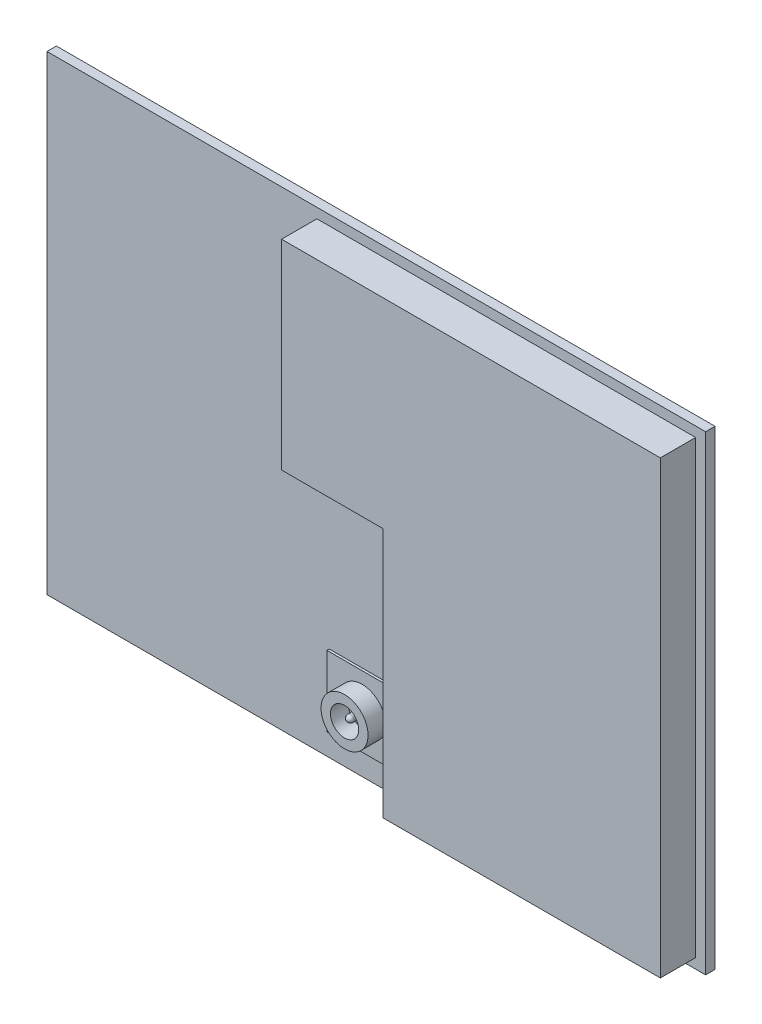
SolidWorks part; units mm, degrees
ref_plane "Front Plane" through (0, 0, 0) normal (0, 0, 1) x (1, 0, 0)
ref_plane "Top Plane" through (0, 0, 0) normal (0, 1, 0) x (1, 0, 0)
ref_plane "Right Plane" through (0, 0, 0) normal (1, 0, 0) x (0, 0, -1)
sketch "Sketch1" plane through (0, 0, 0) normal (0, 0, 1) x (1, 0, 0)
  line L1 (0, 0) -> (28, 0)
  line L2 (0, 0) -> (0, 20)
  line L3 (0, 20) -> (28, 20)
  line L4 (28, 0) -> (28, 20)
  dimension "D1" = 28
  dimension "D2" = 20
extrude "Boss-Extrude1" add sketch "Sketch1" along normal blind 0.4
sketch "Sketch2" plane through (0, 0, 0.4) normal (0, 0, 1) x (1, 0, 0)
  line L0 (11.475, 11.075) -> (15.775, 11.075)
  line L1 (27.575, 19.575) -> (11.475, 19.575)
  line L2 (27.575, 19.575) -> (27.575, 0.425)
  line L3 (27.575, 0.425) -> (15.775, 0.425)
  line L4 (11.475, 19.575) -> (11.475, 11.075)
  line L5 (15.775, 11.075) -> (15.775, 0.425)
  line L6 (0, 10) -> (28, 10) construction
  line L7 (0, 20) -> (0, 0) construction
  line L8 (28, 0) -> (28, 20) construction
  point P12 (27.575, 10)
  dimension "D1" = 19.15
  dimension "D2" = 11.8
  dimension "D3" = 0.425
  dimension "D4" = 16.1
  dimension "D5" = 8.5
extrude "Boss-Extrude2" add sketch "Sketch2" along normal blind 1.5
sketch "Sketch3" plane through (0, 0, 0.4) normal (0, 0, 1) x (1, 0, 0)
  line L0 (0, 0) -> (28, 0) construction
  line L1 (12, 4) -> (15, 4)
  line L2 (12, 4) -> (12, 1)
  line L3 (12, 1) -> (15, 1)
  line L4 (15, 4) -> (15, 1)
  line L5 (0, 20) -> (0, 0) construction
  dimension "D1" = 3
  dimension "D2" = 3
  dimension "D3" = 1
  dimension "D4" = 12
extrude "Boss-Extrude3" add sketch "Sketch3" along normal blind 0.1
sketch "Sketch4" plane through (0, 0, 0.5) normal (0, 0, 1) x (1, 0, 0)
  line L0 (13.5, 4) -> (13.5, 1) construction
  line L1 (15, 4) -> (12, 4) construction
  line L2 (12, 1) -> (15, 1) construction
  circle A0 centre (13.5, 2.5) radius 1
  circle A1 centre (13.5, 2.5) radius 0.6
  dimension "D1" = 2
  dimension "D2" = 1.2
extrude "Boss-Extrude4" add sketch "Sketch4" along normal blind 0.75
sketch "Sketch5" plane through (0, 0, 0.5) normal (0, 0, 1) x (1, 0, 0)
  circle A0 centre (13.5, 2.5) radius 0.15
  dimension "D1" = 0.3
extrude "Boss-Extrude5" add sketch "Sketch5" along normal blind 0.65
fillet "Fillet1" radius 0.15 1 edges at (13.65, 2.5, 1.15)
sketch "Sketch6" plane through (0, 0, 0) normal (0, 0, -1) x (-1, 0, 0)
  line L0 (0, 0) -> (-28, 0) construction
  line L1 (-12.8, 0.3) -> (-12.2, 0.3)
  line L2 (-12.8, 0.3) -> (-12.8, 1.1)
  line L3 (-12.8, 1.1) -> (-12.2, 1.1)
  line L4 (-12.2, 0.3) -> (-12.2, 1.1)
  line L5 (-28, 0) -> (-28, 20) construction
  line L6 (0, 20) -> (0, 0) construction
  line L7 (-13.8, 0.3) -> (-13.2, 0.3)
  line L8 (-13.8, 0.3) -> (-13.8, 1.1)
  line L9 (-13.8, 1.1) -> (-13.2, 1.1)
  line L10 (-13.2, 0.3) -> (-13.2, 1.1)
  line L11 (-14.8, 0.3) -> (-14.2, 0.3)
  line L12 (-14.8, 0.3) -> (-14.8, 1.1)
  line L13 (-14.8, 1.1) -> (-14.2, 1.1)
  line L14 (-14.2, 0.3) -> (-14.2, 1.1)
  line L15 (-15.8, 0.3) -> (-15.2, 0.3)
  line L16 (-15.8, 0.3) -> (-15.8, 1.1)
  line L17 (-15.8, 1.1) -> (-15.2, 1.1)
  line L18 (-15.2, 0.3) -> (-15.2, 1.1)
  line L19 (-16.8, 0.3) -> (-16.2, 0.3)
  line L20 (-16.8, 0.3) -> (-16.8, 1.1)
  line L21 (-16.8, 1.1) -> (-16.2, 1.1)
  line L22 (-16.2, 0.3) -> (-16.2, 1.1)
  line L23 (-17.8, 0.3) -> (-17.2, 0.3)
  line L24 (-17.8, 0.3) -> (-17.8, 1.1)
  line L25 (-17.8, 1.1) -> (-17.2, 1.1)
  line L26 (-17.2, 0.3) -> (-17.2, 1.1)
  line L27 (-18.8, 0.3) -> (-18.2, 0.3)
  line L28 (-18.8, 0.3) -> (-18.8, 1.1)
  line L29 (-18.8, 1.1) -> (-18.2, 1.1)
  line L30 (-18.2, 0.3) -> (-18.2, 1.1)
  line L31 (-19.8, 0.3) -> (-19.2, 0.3)
  line L32 (-19.8, 0.3) -> (-19.8, 1.1)
  line L33 (-19.8, 1.1) -> (-19.2, 1.1)
  line L34 (-19.2, 0.3) -> (-19.2, 1.1)
  line L35 (-20.8, 0.3) -> (-20.2, 0.3)
  line L36 (-20.8, 0.3) -> (-20.8, 1.1)
  line L37 (-20.8, 1.1) -> (-20.2, 1.1)
  line L38 (-20.2, 0.3) -> (-20.2, 1.1)
  line L39 (-21.8, 0.3) -> (-21.2, 0.3)
  line L40 (-21.8, 0.3) -> (-21.8, 1.1)
  line L41 (-21.8, 1.1) -> (-21.2, 1.1)
  line L42 (-21.2, 0.3) -> (-21.2, 1.1)
  line L43 (-22.8, 0.3) -> (-22.2, 0.3)
  line L44 (-22.8, 0.3) -> (-22.8, 1.1)
  line L45 (-22.8, 1.1) -> (-22.2, 1.1)
  line L46 (-22.2, 0.3) -> (-22.2, 1.1)
  line L47 (-23.8, 0.3) -> (-23.2, 0.3)
  line L48 (-23.8, 0.3) -> (-23.8, 1.1)
  line L49 (-23.8, 1.1) -> (-23.2, 1.1)
  line L50 (-23.2, 0.3) -> (-23.2, 1.1)
  line L51 (-24.8, 0.3) -> (-24.2, 0.3)
  line L52 (-24.8, 0.3) -> (-24.8, 1.1)
  line L53 (-24.8, 1.1) -> (-24.2, 1.1)
  line L54 (-24.2, 0.3) -> (-24.2, 1.1)
  line L55 (-25.8, 0.3) -> (-25.2, 0.3)
  line L56 (-25.8, 0.3) -> (-25.8, 1.1)
  line L57 (-25.8, 1.1) -> (-25.2, 1.1)
  line L58 (-25.2, 0.3) -> (-25.2, 1.1)
  line L59 (-26.8, 0.3) -> (-26.2, 0.3)
  line L60 (-26.8, 0.3) -> (-26.8, 1.1)
  line L61 (-26.8, 1.1) -> (-26.2, 1.1)
  line L62 (-26.2, 0.3) -> (-26.2, 1.1)
  line L63 (-13.8, 18.9) -> (-13.2, 18.9)
  line L64 (-13.8, 18.9) -> (-13.8, 19.7)
  line L65 (-13.8, 19.7) -> (-13.2, 19.7)
  line L66 (-13.2, 18.9) -> (-13.2, 19.7)
  line L67 (-14.8, 18.9) -> (-14.2, 18.9)
  line L68 (-14.8, 18.9) -> (-14.8, 19.7)
  line L69 (-14.8, 19.7) -> (-14.2, 19.7)
  line L70 (-14.2, 18.9) -> (-14.2, 19.7)
  line L71 (-15.8, 18.9) -> (-15.2, 18.9)
  line L72 (-15.8, 18.9) -> (-15.8, 19.7)
  line L73 (-15.8, 19.7) -> (-15.2, 19.7)
  line L74 (-15.2, 18.9) -> (-15.2, 19.7)
  line L75 (-16.8, 18.9) -> (-16.2, 18.9)
  line L76 (-16.8, 18.9) -> (-16.8, 19.7)
  line L77 (-16.8, 19.7) -> (-16.2, 19.7)
  line L78 (-16.2, 18.9) -> (-16.2, 19.7)
  line L79 (-17.8, 18.9) -> (-17.2, 18.9)
  line L80 (-17.8, 18.9) -> (-17.8, 19.7)
  line L81 (-17.8, 19.7) -> (-17.2, 19.7)
  line L82 (-17.2, 18.9) -> (-17.2, 19.7)
  line L83 (-18.8, 18.9) -> (-18.2, 18.9)
  line L84 (-18.8, 18.9) -> (-18.8, 19.7)
  line L85 (-18.8, 19.7) -> (-18.2, 19.7)
  line L86 (-18.2, 18.9) -> (-18.2, 19.7)
  line L87 (-19.8, 18.9) -> (-19.2, 18.9)
  line L88 (-19.8, 18.9) -> (-19.8, 19.7)
  line L89 (-19.8, 19.7) -> (-19.2, 19.7)
  line L90 (-19.2, 18.9) -> (-19.2, 19.7)
  line L91 (-20.8, 18.9) -> (-20.2, 18.9)
  line L92 (-20.8, 18.9) -> (-20.8, 19.7)
  line L93 (-20.8, 19.7) -> (-20.2, 19.7)
  line L94 (-20.2, 18.9) -> (-20.2, 19.7)
  line L95 (-21.8, 18.9) -> (-21.2, 18.9)
  line L96 (-21.8, 18.9) -> (-21.8, 19.7)
  line L97 (-21.8, 19.7) -> (-21.2, 19.7)
  line L98 (-21.2, 18.9) -> (-21.2, 19.7)
  line L99 (-22.8, 18.9) -> (-22.2, 18.9)
  line L100 (-22.8, 18.9) -> (-22.8, 19.7)
  line L101 (-22.8, 19.7) -> (-22.2, 19.7)
  line L102 (-22.2, 18.9) -> (-22.2, 19.7)
  line L103 (-23.8, 18.9) -> (-23.2, 18.9)
  line L104 (-23.8, 18.9) -> (-23.8, 19.7)
  line L105 (-23.8, 19.7) -> (-23.2, 19.7)
  line L106 (-23.2, 18.9) -> (-23.2, 19.7)
  line L107 (-24.8, 18.9) -> (-24.2, 18.9)
  line L108 (-24.8, 18.9) -> (-24.8, 19.7)
  line L109 (-24.8, 19.7) -> (-24.2, 19.7)
  line L110 (-24.2, 18.9) -> (-24.2, 19.7)
  line L111 (-25.8, 18.9) -> (-25.2, 18.9)
  line L112 (-25.8, 18.9) -> (-25.8, 19.7)
  line L113 (-25.8, 19.7) -> (-25.2, 19.7)
  line L114 (-25.2, 18.9) -> (-25.2, 19.7)
  line L115 (-26.8, 18.9) -> (-26.2, 18.9)
  line L116 (-26.8, 18.9) -> (-26.8, 19.7)
  line L117 (-26.8, 19.7) -> (-26.2, 19.7)
  line L118 (-26.2, 18.9) -> (-26.2, 19.7)
  line L119 (-12.8, 18.9) -> (-12.2, 18.9)
  line L120 (-12.8, 18.9) -> (-12.8, 19.7)
  line L121 (-12.8, 19.7) -> (-12.2, 19.7)
  line L122 (-12.2, 18.9) -> (-12.2, 19.7)
  line L123 (-27.7, 2.3) -> (-26.9, 2.3)
  line L124 (-27.7, 2.3) -> (-27.7, 1.7)
  line L125 (-27.7, 1.7) -> (-26.9, 1.7)
  line L126 (-26.9, 2.3) -> (-26.9, 1.7)
  line L127 (-12.2, 2.3) -> (-11.4, 2.3)
  line L128 (-12.2, 2.3) -> (-12.2, 1.7)
  line L129 (-12.2, 1.7) -> (-11.4, 1.7)
  line L130 (-11.4, 2.3) -> (-11.4, 1.7)
  line L131 (-12.2, 3.3) -> (-11.4, 3.3)
  line L132 (-12.2, 3.3) -> (-12.2, 2.7)
  line L133 (-12.2, 2.7) -> (-11.4, 2.7)
  line L134 (-11.4, 3.3) -> (-11.4, 2.7)
  line L135 (-12.2, 4.3) -> (-11.4, 4.3)
  line L136 (-12.2, 4.3) -> (-12.2, 3.7)
  line L137 (-12.2, 3.7) -> (-11.4, 3.7)
  line L138 (-11.4, 4.3) -> (-11.4, 3.7)
  line L139 (-12.2, 5.3) -> (-11.4, 5.3)
  line L140 (-12.2, 5.3) -> (-12.2, 4.7)
  line L141 (-12.2, 4.7) -> (-11.4, 4.7)
  line L142 (-11.4, 5.3) -> (-11.4, 4.7)
  line L143 (-12.2, 6.3) -> (-11.4, 6.3)
  line L144 (-12.2, 6.3) -> (-12.2, 5.7)
  line L145 (-12.2, 5.7) -> (-11.4, 5.7)
  line L146 (-11.4, 6.3) -> (-11.4, 5.7)
  line L147 (-12.2, 7.3) -> (-11.4, 7.3)
  line L148 (-12.2, 7.3) -> (-12.2, 6.7)
  line L149 (-12.2, 6.7) -> (-11.4, 6.7)
  line L150 (-11.4, 7.3) -> (-11.4, 6.7)
  line L151 (-12.2, 8.3) -> (-11.4, 8.3)
  line L152 (-12.2, 8.3) -> (-12.2, 7.7)
  line L153 (-12.2, 7.7) -> (-11.4, 7.7)
  line L154 (-11.4, 8.3) -> (-11.4, 7.7)
  line L155 (-12.2, 9.3) -> (-11.4, 9.3)
  line L156 (-12.2, 9.3) -> (-12.2, 8.7)
  line L157 (-12.2, 8.7) -> (-11.4, 8.7)
  line L158 (-11.4, 9.3) -> (-11.4, 8.7)
  line L159 (-12.2, 10.3) -> (-11.4, 10.3)
  line L160 (-12.2, 10.3) -> (-12.2, 9.7)
  line L161 (-12.2, 9.7) -> (-11.4, 9.7)
  line L162 (-11.4, 10.3) -> (-11.4, 9.7)
  line L163 (-12.2, 11.3) -> (-11.4, 11.3)
  line L164 (-12.2, 11.3) -> (-12.2, 10.7)
  line L165 (-12.2, 10.7) -> (-11.4, 10.7)
  line L166 (-11.4, 11.3) -> (-11.4, 10.7)
  line L167 (-12.2, 12.3) -> (-11.4, 12.3)
  line L168 (-12.2, 12.3) -> (-12.2, 11.7)
  line L169 (-12.2, 11.7) -> (-11.4, 11.7)
  line L170 (-11.4, 12.3) -> (-11.4, 11.7)
  line L171 (-12.2, 13.3) -> (-11.4, 13.3)
  line L172 (-12.2, 13.3) -> (-12.2, 12.7)
  line L173 (-12.2, 12.7) -> (-11.4, 12.7)
  line L174 (-11.4, 13.3) -> (-11.4, 12.7)
  line L175 (-12.2, 14.3) -> (-11.4, 14.3)
  line L176 (-12.2, 14.3) -> (-12.2, 13.7)
  line L177 (-12.2, 13.7) -> (-11.4, 13.7)
  line L178 (-11.4, 14.3) -> (-11.4, 13.7)
  line L179 (-12.2, 15.3) -> (-11.4, 15.3)
  line L180 (-12.2, 15.3) -> (-12.2, 14.7)
  line L181 (-12.2, 14.7) -> (-11.4, 14.7)
  line L182 (-11.4, 15.3) -> (-11.4, 14.7)
  line L183 (-12.2, 16.3) -> (-11.4, 16.3)
  line L184 (-12.2, 16.3) -> (-12.2, 15.7)
  line L185 (-12.2, 15.7) -> (-11.4, 15.7)
  line L186 (-11.4, 16.3) -> (-11.4, 15.7)
  line L187 (-12.2, 17.3) -> (-11.4, 17.3)
  line L188 (-12.2, 17.3) -> (-12.2, 16.7)
  line L189 (-12.2, 16.7) -> (-11.4, 16.7)
  line L190 (-11.4, 17.3) -> (-11.4, 16.7)
  line L191 (-12.2, 18.3) -> (-11.4, 18.3)
  line L192 (-12.2, 18.3) -> (-12.2, 17.7)
  line L193 (-12.2, 17.7) -> (-11.4, 17.7)
  line L194 (-11.4, 18.3) -> (-11.4, 17.7)
  line L195 (-27.7, 3.3) -> (-26.9, 3.3)
  line L196 (-27.7, 3.3) -> (-27.7, 2.7)
  line L197 (-27.7, 2.7) -> (-26.9, 2.7)
  line L198 (-26.9, 3.3) -> (-26.9, 2.7)
  line L199 (-27.7, 4.3) -> (-26.9, 4.3)
  line L200 (-27.7, 4.3) -> (-27.7, 3.7)
  line L201 (-27.7, 3.7) -> (-26.9, 3.7)
  line L202 (-26.9, 4.3) -> (-26.9, 3.7)
  line L203 (-27.7, 5.3) -> (-26.9, 5.3)
  line L204 (-27.7, 5.3) -> (-27.7, 4.7)
  line L205 (-27.7, 4.7) -> (-26.9, 4.7)
  line L206 (-26.9, 5.3) -> (-26.9, 4.7)
  line L207 (-27.7, 6.3) -> (-26.9, 6.3)
  line L208 (-27.7, 6.3) -> (-27.7, 5.7)
  line L209 (-27.7, 5.7) -> (-26.9, 5.7)
  line L210 (-26.9, 6.3) -> (-26.9, 5.7)
  line L211 (-27.7, 7.3) -> (-26.9, 7.3)
  line L212 (-27.7, 7.3) -> (-27.7, 6.7)
  line L213 (-27.7, 6.7) -> (-26.9, 6.7)
  line L214 (-26.9, 7.3) -> (-26.9, 6.7)
  line L215 (-27.7, 8.3) -> (-26.9, 8.3)
  line L216 (-27.7, 8.3) -> (-27.7, 7.7)
  line L217 (-27.7, 7.7) -> (-26.9, 7.7)
  line L218 (-26.9, 8.3) -> (-26.9, 7.7)
  line L219 (-27.7, 9.3) -> (-26.9, 9.3)
  line L220 (-27.7, 9.3) -> (-27.7, 8.7)
  line L221 (-27.7, 8.7) -> (-26.9, 8.7)
  line L222 (-26.9, 9.3) -> (-26.9, 8.7)
  line L223 (-27.7, 10.3) -> (-26.9, 10.3)
  line L224 (-27.7, 10.3) -> (-27.7, 9.7)
  line L225 (-27.7, 9.7) -> (-26.9, 9.7)
  line L226 (-26.9, 10.3) -> (-26.9, 9.7)
  line L227 (-27.7, 11.3) -> (-26.9, 11.3)
  line L228 (-27.7, 11.3) -> (-27.7, 10.7)
  line L229 (-27.7, 10.7) -> (-26.9, 10.7)
  line L230 (-26.9, 11.3) -> (-26.9, 10.7)
  line L231 (-27.7, 12.3) -> (-26.9, 12.3)
  line L232 (-27.7, 12.3) -> (-27.7, 11.7)
  line L233 (-27.7, 11.7) -> (-26.9, 11.7)
  line L234 (-26.9, 12.3) -> (-26.9, 11.7)
  line L235 (-27.7, 13.3) -> (-26.9, 13.3)
  line L236 (-27.7, 13.3) -> (-27.7, 12.7)
  line L237 (-27.7, 12.7) -> (-26.9, 12.7)
  line L238 (-26.9, 13.3) -> (-26.9, 12.7)
  line L239 (-27.7, 14.3) -> (-26.9, 14.3)
  line L240 (-27.7, 14.3) -> (-27.7, 13.7)
  line L241 (-27.7, 13.7) -> (-26.9, 13.7)
  line L242 (-26.9, 14.3) -> (-26.9, 13.7)
  line L243 (-27.7, 15.3) -> (-26.9, 15.3)
  line L244 (-27.7, 15.3) -> (-27.7, 14.7)
  line L245 (-27.7, 14.7) -> (-26.9, 14.7)
  line L246 (-26.9, 15.3) -> (-26.9, 14.7)
  line L247 (-27.7, 16.3) -> (-26.9, 16.3)
  line L248 (-27.7, 16.3) -> (-27.7, 15.7)
  line L249 (-27.7, 15.7) -> (-26.9, 15.7)
  line L250 (-26.9, 16.3) -> (-26.9, 15.7)
  line L251 (-27.7, 17.3) -> (-26.9, 17.3)
  line L252 (-27.7, 17.3) -> (-27.7, 16.7)
  line L253 (-27.7, 16.7) -> (-26.9, 16.7)
  line L254 (-26.9, 17.3) -> (-26.9, 16.7)
  line L255 (-27.7, 18.3) -> (-26.9, 18.3)
  line L256 (-27.7, 18.3) -> (-27.7, 17.7)
  line L257 (-27.7, 17.7) -> (-26.9, 17.7)
  line L258 (-26.9, 18.3) -> (-26.9, 17.7)
  line L259 (-20, 14) -> (-19, 14)
  line L260 (-17, 14) -> (-16, 14)
  line L261 (-17, 14) -> (-17, 13)
  line L262 (-17, 13) -> (-16, 13)
  line L263 (-16, 14) -> (-16, 13)
  line L264 (-20, 14) -> (-20, 13)
  line L265 (-20, 13) -> (-19, 13)
  line L266 (-19, 14) -> (-19, 13)
  line L267 (-23, 14) -> (-22, 14)
  line L268 (-23, 14) -> (-23, 13)
  line L269 (-23, 13) -> (-22, 13)
  line L270 (-22, 14) -> (-22, 13)
  line L271 (-20, 10.5) -> (-19, 10.5)
  line L272 (-20, 10.5) -> (-20, 9.5)
  line L273 (-20, 9.5) -> (-19, 9.5)
  line L274 (-19, 10.5) -> (-19, 9.5)
  line L275 (-23, 10.5) -> (-22, 10.5)
  line L276 (-23, 10.5) -> (-23, 9.5)
  line L277 (-23, 9.5) -> (-22, 9.5)
  line L278 (-22, 10.5) -> (-22, 9.5)
  line L279 (-20, 7) -> (-19, 7)
  line L280 (-20, 7) -> (-20, 6)
  line L281 (-20, 6) -> (-19, 6)
  line L282 (-19, 7) -> (-19, 6)
  line L283 (-23, 7) -> (-22, 7)
  line L284 (-23, 7) -> (-23, 6)
  line L285 (-23, 6) -> (-22, 6)
  line L286 (-22, 7) -> (-22, 6)
  line L287 (-17, 10.5) -> (-16, 10.5)
  line L288 (-17, 10.5) -> (-17, 9.5)
  line L289 (-17, 9.5) -> (-16, 9.5)
  line L290 (-16, 10.5) -> (-16, 9.5)
  line L291 (-17, 7) -> (-16, 7)
  line L292 (-17, 7) -> (-17, 6)
  line L293 (-17, 6) -> (-16, 6)
  line L294 (-16, 7) -> (-16, 6)
  line L295 (-0.38, 19.62) -> (-1.38, 19.62)
  line L296 (-0.38, 1.38) -> (-1.38, 1.38)
  line L297 (-0.38, 1.38) -> (-0.38, 0.38)
  line L298 (-0.38, 0.38) -> (-1.38, 0.38)
  line L299 (-1.38, 1.38) -> (-1.38, 0.38)
  line L300 (-0.38, 19.62) -> (-0.38, 18.62)
  line L301 (-0.38, 18.62) -> (-1.38, 18.62)
  line L302 (-1.38, 19.62) -> (-1.38, 18.62)
  line L303 (-28, 20) -> (0, 20) construction
  point P266 (-28, 10)
  dimension "D1" = 0.8
  dimension "D2" = 0.6
  dimension "D3" = 0.3
  dimension "D4" = 12.2
  dimension "D5" = 15
  dimension "D6" = 2
  dimension "D7" = 0.4
  dimension "D8" = 0.3
  dimension "D9" = 17.8
  dimension "D10" = 12.2
  dimension "D11" = 1.1
  dimension "D12" = 0.8
  dimension "D13" = 0.6
  dimension "D14" = 1.7
  dimension "D17" = 1
  dimension "D18" = 0.3
  dimension "D19" = 11.4
  dimension "D20" = 1.7
  dimension "D21" = 1
  dimension "D22" = 1
  dimension "D23" = 11.9
  dimension "D24" = 10.9
  dimension "D27" = 6
  dimension "D28" = 5
  dimension "D29" = 6
  dimension "D30" = 5
  dimension "D31" = 1
  dimension "D32" = 1
  dimension "D33" = 1.38
  dimension "D34" = 1.38
  dimension "D35" = 2
  dimension "D36" = 0.38
  dimension "D37" = 0.38
  dimension "D15" = 2
  dimension "D16" = 17
  dimension "D25" = 3
  dimension "D26" = 3
extrude "Boss-Extrude6" add sketch "Sketch6" along normal blind 0.1
